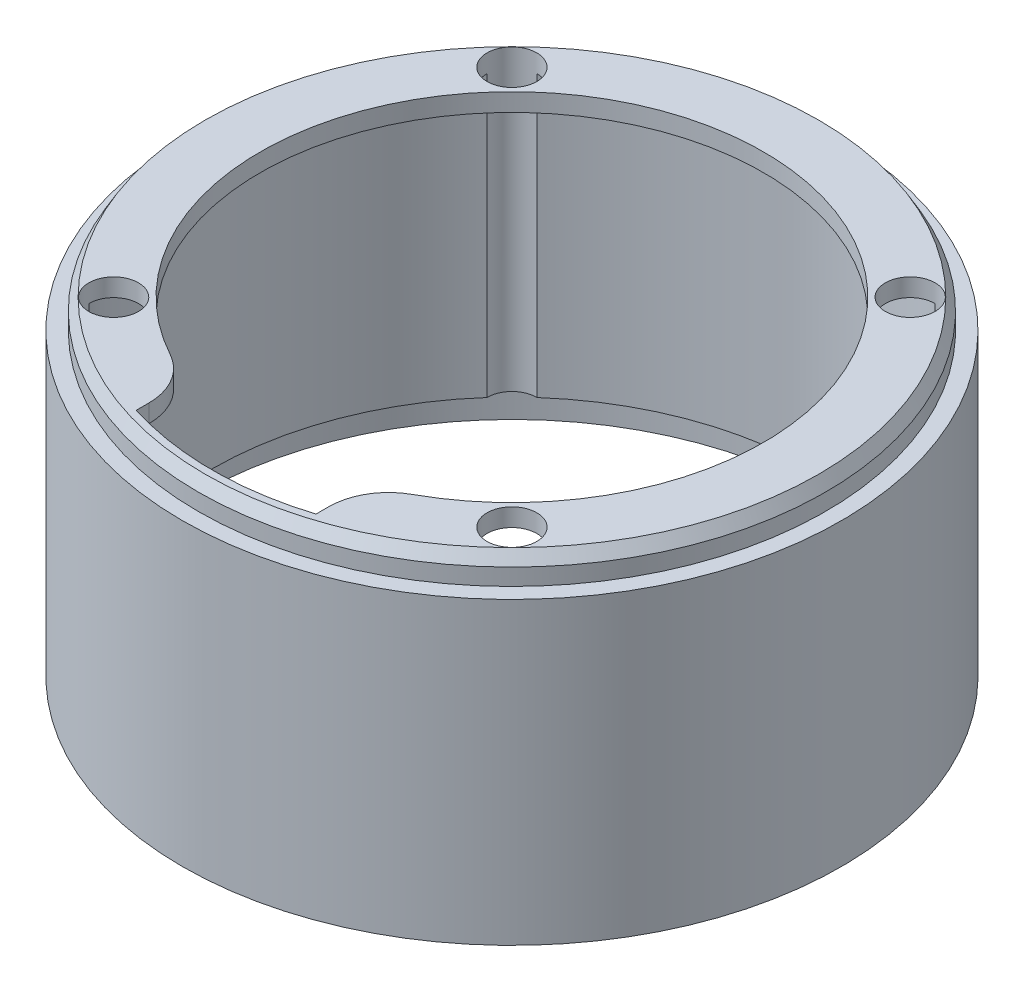
SolidWorks part; units mm, degrees
ref_plane "Спереди" through (0, 0, 0) normal (0, 0, 1) x (1, 0, 0)
ref_plane "Сверху" through (0, 0, 0) normal (0, 1, 0) x (1, 0, 0)
ref_plane "Справа" through (0, 0, 0) normal (1, 0, 0) x (0, 0, -1)
sketch "Sketch1" plane through (0, 0, 0) normal (0, 1, 0) x (1, 0, 0)
  circle A0 centre (0, 0) radius 55
  dimension "D1" = 110
extrude "Boss-Extrude1" add sketch "Sketch1" along normal blind 54.8
shell "Shell1" thickness 5
sketch "Sketch2" plane through (0, 49.8, 0) normal (0, -1, 0) x (1, 0, 0)
  circle A0 centre (0, 0) radius 35
  dimension "D1" = 70
extrude "Cut-Extrude1" cut sketch "Sketch2" against normal through all
sketch "Sketch3" plane through (0, 54.8, 0) normal (0, 1, 0) x (1, 0, 0)
  circle A0 centre (0, 0) radius 42
  dimension "D1" = 84
extrude "Cut-Extrude2" cut sketch "Sketch3" against normal through all
sketch "Sketch4" plane through (0, 54.8, 0) normal (0, 1, 0) x (1, 0, 0)
  line L1 (-33.234, 33.234) -> (33.234, 33.234) construction
  line L2 (-33.234, 33.234) -> (-33.234, -33.234) construction
  line L3 (-33.234, -33.234) -> (33.234, -33.234) construction
  line L4 (33.234, 33.234) -> (33.234, -33.234) construction
  line L5 (-33.234, 33.234) -> (33.234, -33.234) construction
  line L6 (-33.234, -33.234) -> (33.234, 33.234) construction
  circle A0 centre (0, 0) radius 55 construction
  circle A2 centre (-33.234, -33.234) radius 4.15
  circle A3 centre (-33.234, 33.234) radius 4.15
  circle A4 centre (33.234, 33.234) radius 4.15
  circle A5 centre (33.234, -33.234) radius 4.15
  circle A6 centre (0, 0) radius 47 construction
  dimension "D2" = 8.3
  dimension "D3" = 8
extrude "Cut-Extrude3" cut sketch "Sketch4" against normal through all
sketch "Sketch6" plane through (0, 49.8, 0) normal (0, -1, 0) x (1, 0, 0)
  circle A0 centre (0, 0) radius 50
extrude "Cut-Extrude4" cut sketch "Sketch6" against normal blind 2
sketch "Sketch7" plane through (0, 51.8, 0) normal (0, -1, 0) x (1, 0, 0)
  line L0 (33.234, 33.234) -> (-33.234, 33.234) construction
  line L1 (0, 33.234) -> (0, 50) construction
  line L2 (15, 33.234) -> (15, 47.697)
  line L3 (-15, 33.234) -> (-15, 47.697)
  line L4 (15, 33.234) -> (-15, 33.234)
  arc A0 (33.2031, 37.3839) -> (-33.2031, 37.3839) centre (0, 0) ccw construction
  arc A1 (15, 47.697) -> (-15, 47.697) centre (0, 0) ccw
  point P14 (0, 33.234)
  dimension "D1" = 30
extrude "Cut-Extrude5" cut sketch "Sketch7" against normal through all
fillet "Fillet1" radius 10 2 edges at (-15, 53.3, 39.2301) (15, 53.3, 39.2301)
sketch "Sketch8" plane through (0, 54.8, 0) normal (0, 1, 0) x (1, 0, 0)
  circle A0 centre (0, 0) radius 52.35
  dimension "D1" = 104.7
extrude "Cut-Extrude6" cut sketch "Sketch8" against normal blind 4.8 flip side to cut
chamfer "Chamfer1" distance 2 angle 30 1 edges at (0, 54.8, 52.35)
sketch "Sketch9" plane through (0, 0, 0) normal (0, -1, 0) x (1, 0, 0)
  circle A0 centre (0, 0) radius 52.5
  dimension "D1" = 105
extrude "Cut-Extrude7" cut sketch "Sketch9" against normal blind 5
